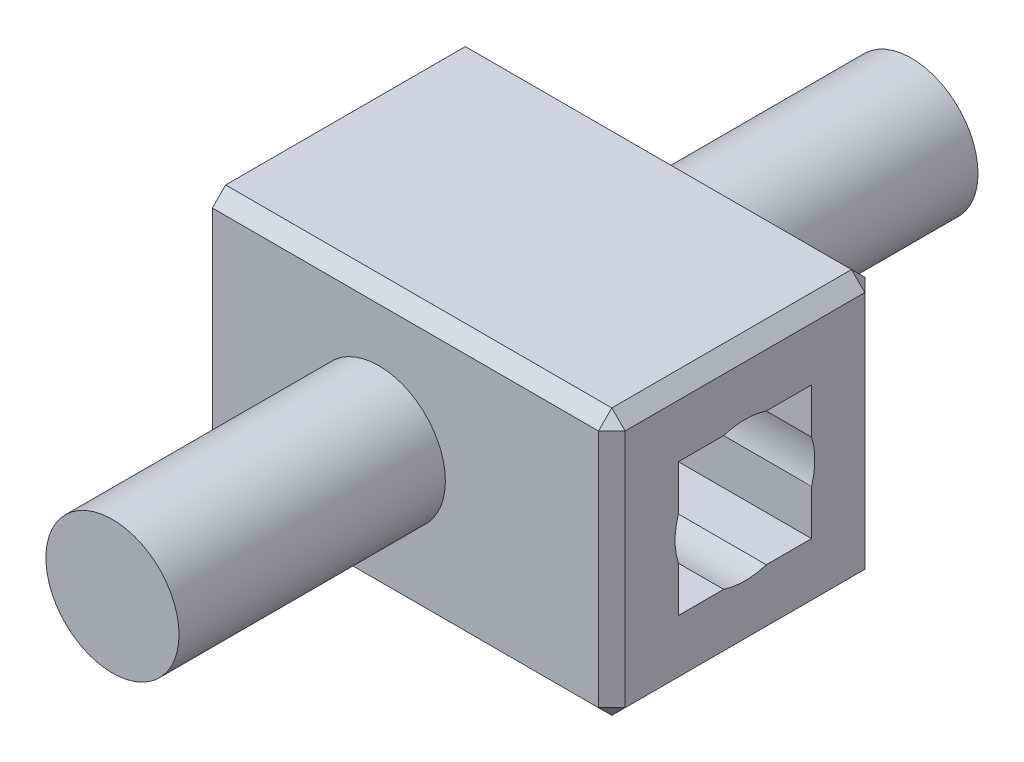
SolidWorks part; units mm, degrees
material "Fundición maleable"
ref_plane "Alzado" through (0, 0, 0) normal (0, 0, 1) x (1, 0, 0)
ref_plane "Planta" through (0, 0, 0) normal (0, 1, 0) x (1, 0, 0)
ref_plane "Vista lateral" through (0, 0, 0) normal (1, 0, 0) x (0, 0, -1)
sketch "Croquis1" plane through (0, 0, 0) normal (0, 0, 1) x (1, 0, 0)
  line L1 (-125, 100) -> (125, 100)
  line L2 (-125, 100) -> (-125, -100)
  line L3 (-125, -100) -> (125, -100)
  line L5 (-125, 100) -> (125, -100) construction
  line L6 (-125, -100) -> (125, 100) construction
  line L7 (125, 100) -> (175, 100)
  line L9 (125, -100) -> (175, -100)
  line L10 (175, 100) -> (175, -100)
  point P0 (0, 0)
  dimension "D1" = 250
  dimension "D2" = 200
  dimension "D3" = 50
extrude "Saliente-Extruir1" add sketch "Croquis1" along normal blind 200
sketch "Croquis2" plane through (0, 0, 200) normal (0, 0, 1) x (1, 0, 0)
  circle A0 centre (0, 0) radius 50
  dimension "D1" = 100
extrude "Saliente-Extruir2" add sketch "Croquis2" along normal blind 200 and the other way blind 400
sketch "Croquis3" plane through (175, 0, 0) normal (1, 0, 0) x (0, 0, -1)
  line L0 (-200, -100) -> (0, 100) construction
  line L2 (-150, 50) -> (-50, 50)
  line L3 (-150, 50) -> (-150, -50)
  line L4 (-150, -50) -> (-50, -50)
  line L5 (-50, 50) -> (-50, -50)
  line L6 (-150, 50) -> (-50, -50) construction
  line L7 (-150, -50) -> (-50, 50) construction
  point P4 (-100, 0)
  dimension "D1" = 100
  dimension "D2" = 100
extrude "Cortar-Extruir1" cut sketch "Croquis3" against normal through all
sketch "Croquis4" plane through (175, 0, 0) normal (1, 0, 0) x (0, 0, -1)
  line L0 (-150, -50) -> (-50, 50) construction
  circle A0 centre (-100, 0) radius 52.5
  dimension "D1" = 105
extrude "Cortar-Extruir2" cut sketch "Croquis4" against normal through all
chamfer "Chaflán1" distance 10 angle 45 8 edges at (25, -100, 200) (25, -100, 0) (175, -100, 100) (175, 0, 0) (175, 0, 200) (25, 100, 200) (175, 100, 100) (25, 100, 0)
